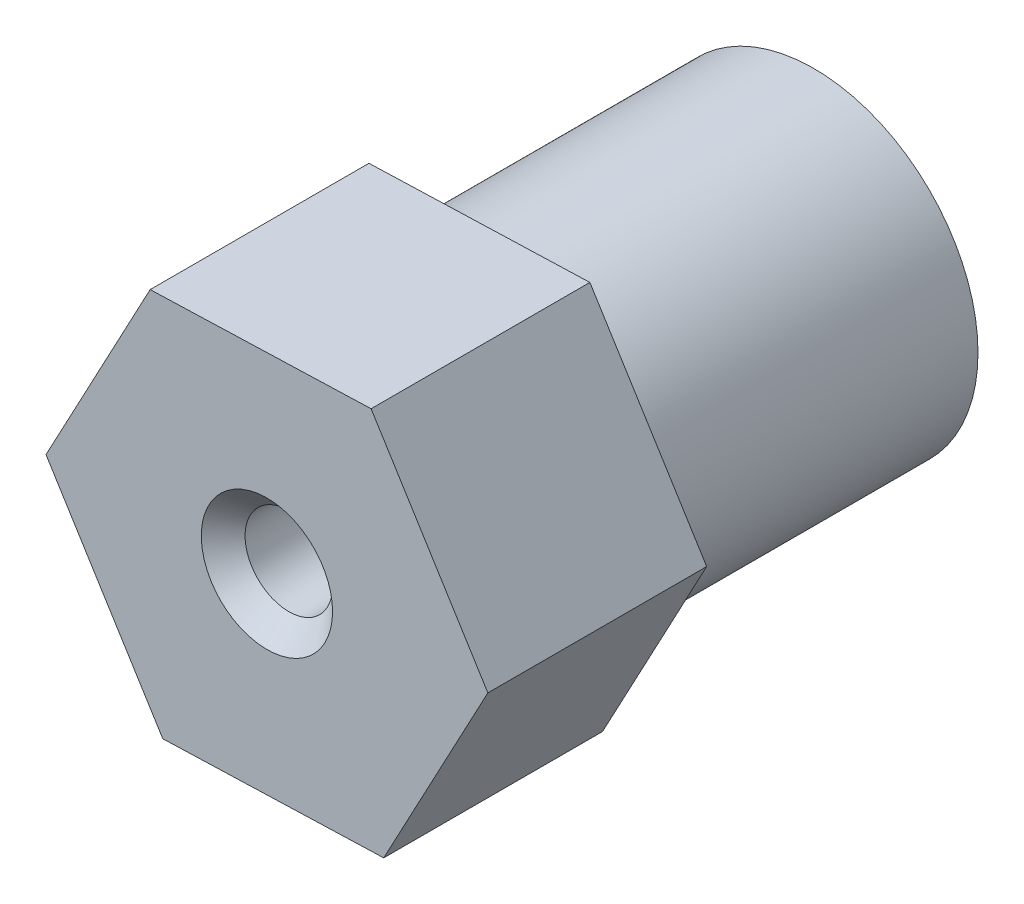
SolidWorks part; units mm, degrees
material "Plain Carbon Steel"
ref_plane "Front Plane" through (0, 0, 0) normal (0, 0, 1) x (1, 0, 0)
ref_plane "Top Plane" through (0, 0, 0) normal (0, 1, 0) x (1, 0, 0)
ref_plane "Right Plane" through (0, 0, 0) normal (1, 0, 0) x (0, 0, -1)
sketch "Sketch1" plane through (0, 0, 0) normal (0, 0, 1) x (1, 0, 0)
  circle A0 centre (0, 0) radius 4.7625
  circle A1 centre (0, 0) radius 2.54
extrude "Boss-Extrude1" add sketch "Sketch1" along normal blind 9.525
sketch "Sketch2" plane through (0, 0, 9.525) normal (0, 0, 1) x (1, 0, 0)
  line L1 (3.023, 5.659) -> (-3.3894, 5.4475)
  line L2 (-3.3894, 5.4475) -> (-6.4123, -0.2115)
  line L3 (-6.4123, -0.2115) -> (-3.023, -5.659)
  line L4 (-3.023, -5.659) -> (3.3894, -5.4475)
  line L5 (3.3894, -5.4475) -> (6.4123, 0.2115)
  line L6 (6.4123, 0.2115) -> (3.023, 5.659)
  circle A0 centre (0, 0) radius 5.5562 construction
  dimension "D1" = 11.1125
extrude "Boss-Extrude2" add sketch "Sketch2" along normal blind 6.35
sketch "Sketch3" plane through (0, 0, 15.875) normal (0, 0, 1) x (1, 0, 0)
  circle A0 centre (0, 0) radius 1.27
extrude "Cut-Extrude1" cut sketch "Sketch3" against normal up to next
chamfer "Chamfer1" distance 0.635 angle 45 1 edges at (1.27, 0, 15.875)
